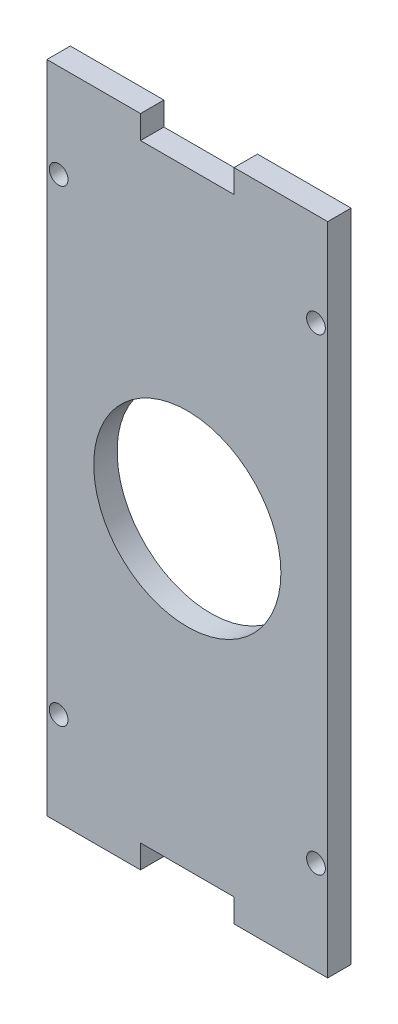
SolidWorks part; units mm, degrees
ref_plane "Front Plane" through (0, 0, 0) normal (0, 0, 1) x (1, 0, 0)
ref_plane "Top Plane" through (0, 0, 0) normal (0, 1, 0) x (1, 0, 0)
ref_plane "Right Plane" through (0, 0, 0) normal (1, 0, 0) x (0, 0, -1)
sketch "Sketch2" plane through (0, 0, 0) normal (0, 0, 1) x (1, 0, 0)
  line L0 (5, 70) -> (5, -70) construction
  line L1 (-25, 70) -> (35, 70)
  line L2 (-25, 70) -> (-25, -70)
  line L3 (-25, -70) -> (-5, -70)
  line L4 (35, 70) -> (35, -70)
  line L5 (-25, 70) -> (35, -70) construction
  line L6 (-25, -70) -> (35, 70) construction
  line L7 (-25, 0) -> (35, 0) construction
  line L8 (-5, 70) -> (-5, 65)
  line L9 (15, 70) -> (15, 65)
  line L10 (15, -70) -> (35, -70)
  line L11 (-5, -65) -> (15, -65)
  line L12 (15, -65) -> (15, -70)
  line L13 (-5, -65) -> (-5, -70)
  line L14 (-5, 65) -> (15, 65)
  point P0 (5, 0)
  point P17 (5, 65)
  dimension "D1" = 140
  dimension "D2" = 60
  dimension "D3" = 5
  dimension "D4" = 20
  dimension "D5" = 20
extrude "Boss-Extrude1" add sketch "Sketch2" along normal blind 5 contours L14 L8 L1 L2 L3 L13 L11 L12 L10 L4 L9
sketch "Sketch3" plane through (0, 0, 5) normal (0, 0, 1) x (1, 0, 0)
  line L0 (-25, 70) -> (-25, -70) construction
  line L1 (-25, 70) -> (-5, 70) construction
  circle A0 centre (-22.5, 50) radius 2
  circle A1 centre (-22.5, -50) radius 2
  dimension "D1" = 4
  dimension "D5" = 2.5
  dimension "D2" = 2.5
  dimension "D3" = 50
  dimension "D6" = 20
  dimension "D7" = 120
  dimension "D4" = 2
extrude "Cut-Extrude1" cut sketch "Sketch3" against normal blind 10
ref_plane "Plane1" through (5, 0, 0) normal (-1, 0, 0) x (0, 0, 1)
mirror "Mirror1" about plane through (5, 0, 0) normal (-1, 0, 0) of "Cut-Extrude1"
sketch "Sketch4" plane through (0, 0, 5) normal (0, 0, 1) x (1, 0, 0)
  circle A0 centre (5, 0) radius 20
  point P2 (0, 0)
  dimension "D1" = 5
  dimension "D2" = 40
extrude "Cut-Extrude2" cut sketch "Sketch4" against normal blind 300
